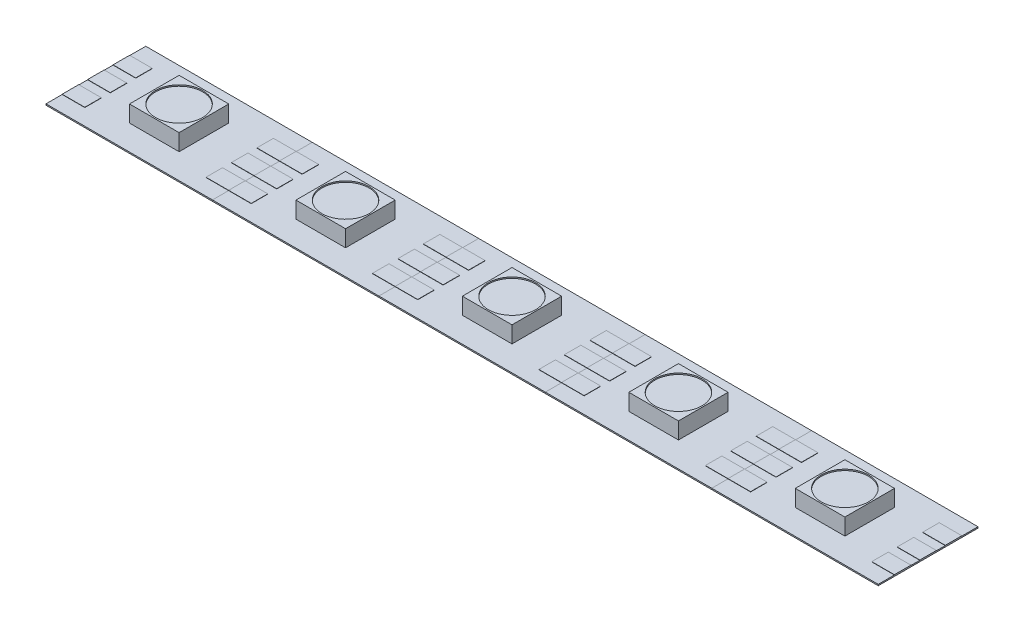
SolidWorks part; units mm, degrees
ref_plane "Front Plane" through (0, 0, 0) normal (0, 0, 1) x (1, 0, 0)
ref_plane "Top Plane" through (0, 0, 0) normal (0, 1, 0) x (1, 0, 0)
ref_plane "Right Plane" through (0, 0, 0) normal (1, 0, 0) x (0, 0, -1)
sketch "Sketch1" plane through (0, 0, 0) normal (0, 1, 0) x (1, 0, 0)
  line L0 (-8.3058, 4.9784) -> (8.3058, -4.9784) construction
  line L1 (-8.3058, 4.9784) -> (8.3058, 4.9784)
  line L2 (-8.3058, 4.9784) -> (-8.3058, -4.9784)
  line L3 (-8.3058, -4.9784) -> (8.3058, -4.9784)
  line L4 (8.3058, 4.9784) -> (8.3058, -4.9784)
  dimension "D1" = 9.9568
  dimension "D2" = 16.6116
extrude "Boss-Extrude1" add sketch "Sketch1" along normal blind 0.127
sketch "Sketch3" plane through (0, 0.127, 0) normal (0, 1, 0) x (1, 0, 0)
  line L0 (-8.3058, 4.9784) -> (8.3058, -4.9784) construction
  line L1 (-2.4765, 2.4765) -> (2.4765, -2.4765) construction
  line L2 (-2.4765, 2.4765) -> (2.4765, 2.4765)
  line L3 (-2.4765, 2.4765) -> (-2.4765, -2.4765)
  line L4 (-2.4765, -2.4765) -> (2.4765, -2.4765)
  line L5 (2.4765, 2.4765) -> (2.4765, -2.4765)
  dimension "D1" = 4.953
extrude "Boss-Extrude3" add sketch "Sketch3" along normal blind 1.651
sketch "Sketch4" plane through (0, 0.127, 0) normal (0, 1, 0) x (1, 0, 0)
  line L0 (-8.3058, 0) -> (8.3058, 0) construction
  line L1 (-8.3058, 4.9784) -> (-8.3058, -4.9784) construction
  line L2 (8.3058, -4.9784) -> (8.3058, 4.9784) construction
  line L3 (-6.047, 0) -> (-8.3058, 0) construction
  line L4 (-8.3058, 0.8255) -> (-6.047, 0.8255)
  line L5 (-8.3058, 0.8255) -> (-8.3058, -0.8255)
  line L6 (-8.3058, -0.8255) -> (-6.047, -0.8255)
  line L7 (-6.047, 0.8255) -> (-6.047, -0.8255)
  line L8 (-8.3058, 3.3655) -> (-6.047, 3.3655)
  line L9 (-6.047, 3.3655) -> (-6.047, 1.7145)
  line L10 (-8.3058, 1.7145) -> (-6.047, 1.7145)
  line L11 (-8.3058, 3.3655) -> (-8.3058, 1.7145)
  line L12 (-6.047, -3.3655) -> (-6.047, -1.7145)
  line L13 (-8.3058, -1.7145) -> (-6.047, -1.7145)
  line L14 (-8.3058, -3.3655) -> (-8.3058, -1.7145)
  line L15 (-8.3058, -3.3655) -> (-6.047, -3.3655)
  line L16 (0, 0) -> (0, -4.9784) construction
  line L17 (-8.3058, -4.9784) -> (8.3058, -4.9784) construction
  line L18 (8.3058, -3.3655) -> (8.3058, -1.7145)
  line L19 (8.3058, -3.3655) -> (6.047, -3.3655)
  line L20 (6.047, -3.3655) -> (6.047, -1.7145)
  line L21 (8.3058, -1.7145) -> (6.047, -1.7145)
  line L22 (8.3058, 0.8255) -> (8.3058, -0.8255)
  line L23 (8.3058, -0.8255) -> (6.047, -0.8255)
  line L24 (6.047, 0.8255) -> (6.047, -0.8255)
  line L25 (8.3058, 0.8255) -> (6.047, 0.8255)
  line L26 (8.3058, 1.7145) -> (6.047, 1.7145)
  line L27 (6.047, 3.3655) -> (6.047, 1.7145)
  line L28 (8.3058, 3.3655) -> (8.3058, 1.7145)
  line L29 (8.3058, 3.3655) -> (6.047, 3.3655)
  dimension "D1" = 1.651
  dimension "D2" = 2
extrude "Boss-Extrude4" add sketch "Sketch4" along normal blind 0.0254
sketch "Sketch5" plane through (0, 1.778, 0) normal (0, 1, 0) x (1, 0, 0)
  circle A0 centre (0, 0) radius 2.3483
extrude "Cut-Extrude1" cut sketch "Sketch5" against normal blind 0.127
pattern_linear "LPattern1" count 5 spacing 16.6116 along (1, 0, 0) of "Boss-Extrude3", "Boss-Extrude4", "Cut-Extrude1", "Boss-Extrude1"
